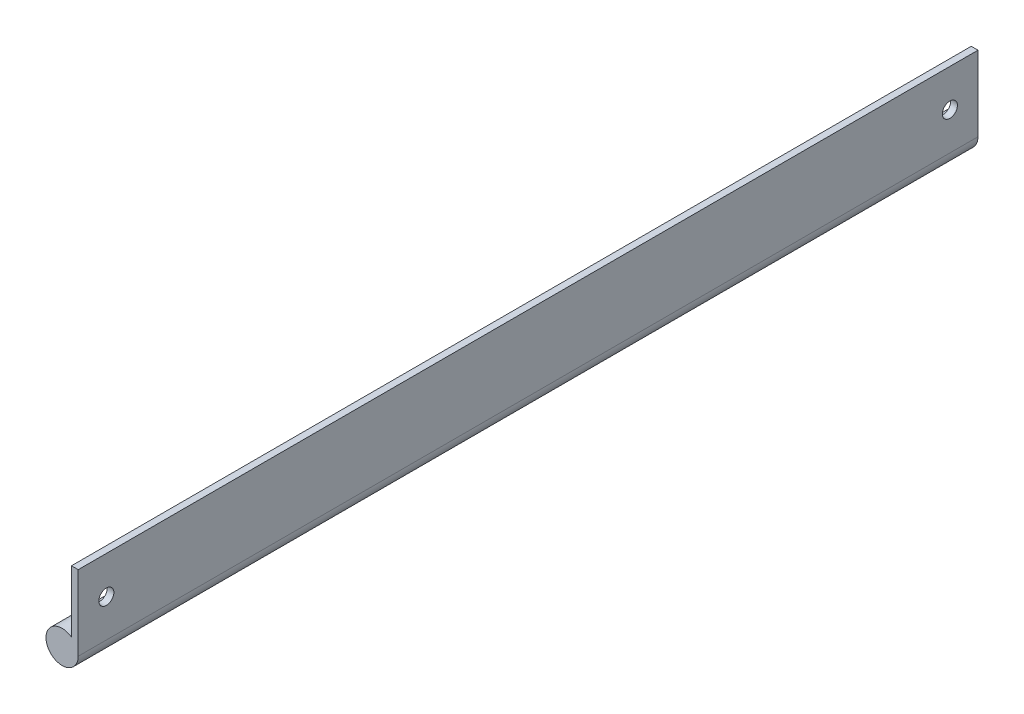
SolidWorks part; units mm, degrees
material "6061-T6 (SS)"
ref_plane "Front Plane" through (0, 0, 0) normal (0, 0, 1) x (1, 0, 0)
ref_plane "Top Plane" through (0, 0, 0) normal (0, 1, 0) x (1, 0, 0)
ref_plane "Right Plane" through (0, 0, 0) normal (1, 0, 0) x (0, 0, -1)
sketch "Sketch1" plane through (0, 0, 0) normal (0, 0, 1) x (1, 0, 0)
  line L2 (-1.143, -8.2568) -> (-1.143, 12.7)
  line L3 (-1.143, 12.7) -> (1.143, 12.7)
  line L4 (1.143, -12.7) -> (1.143, 12.7)
  line L5 (0, 0) -> (1.143, 12.7) construction
  line L6 (-1.143, 12.7) -> (0, 0) construction
  arc A0 (-1.143, -8.2568) -> (1.143, -12.7) centre (-4.318, -12.7) ccw
  point P0 (0, 0)
  dimension "D1" = 2.286
  dimension "D3" = 10.922
  dimension "D2" = 25.4
extrude "Boss-Extrude1" add sketch "Sketch1" along normal blind 304.8
sketch "Sketch2" plane through (-1.143, 0, 0) normal (-1, 0, 0) x (0, 0, 1)
  line L0 (304.8, 0) -> (0, 0) construction
  line L5 (304.8, 12.7) -> (0, 12.7) construction
  line L6 (304.8, 12.7) -> (304.8, -8.2568) construction
  line L7 (0, 12.7) -> (0, -8.2568) construction
  point P9 (9.525, 0)
  point P10 (295.275, 0)
  point P11 (295.275, 0)
  point P13 (304.8, 0)
  dimension "D1" = 9.525
  dimension "D2" = 9.525
  dimension "D3" = 12.7
hole_wizard "#10 Clearance Hole1" positions "Sketch8" profile "Sketch7" hole size "#10" standard "ANSI Inch" end condition through all
sketch "Sketch8" plane through (-1.143, 0, 0) normal (-1, 0, 0) x (0, 0, 1)
  point P0 (9.525, 0)
  point P3 (295.275, 0)
sketch "Sketch7" plane through (-1.143, 0, 9.525) normal (0, 1, 0) x (0, 0, 1)
  line L0 (0, 0) -> (0, 2.286)
  line L1 (0, 2.286) -> (2.5527, 2.286)
  line L2 (2.5527, 2.286) -> (2.5527, 0)
  line L5 (2.5527, 0) -> (0, 0)
  line L11 (0, -6.35) -> (0, 107.95) construction
  dimension "Thru Hole Dia." = 5.1054
  dimension "Thru Hole Depth" = 2.286
